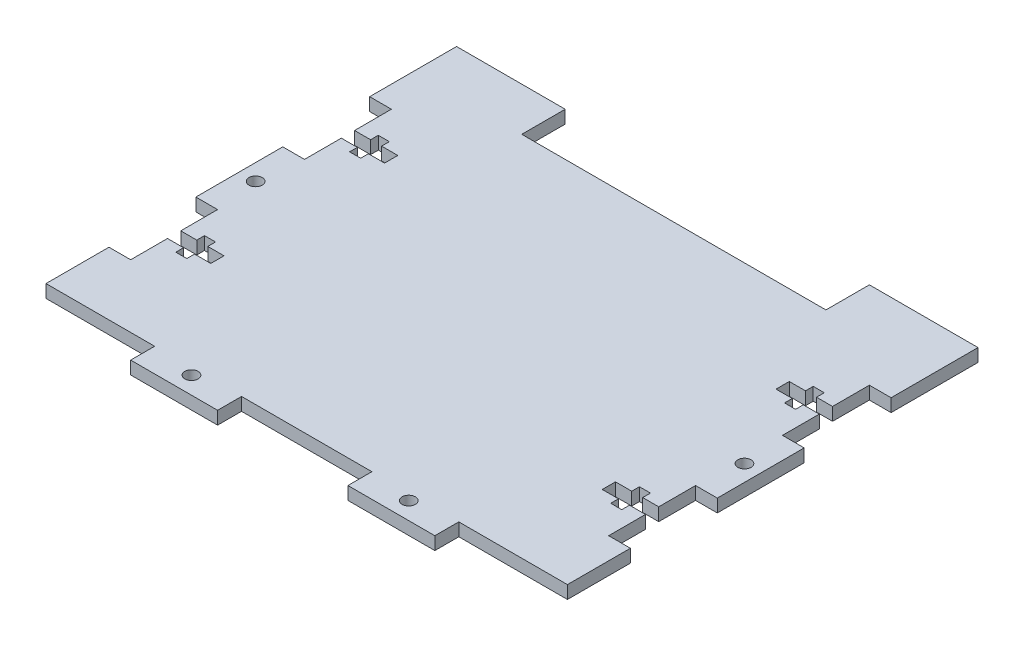
SolidWorks part; units mm, degrees
ref_plane "Front Plane" through (0, 0, 0) normal (0, 0, 1) x (1, 0, 0)
ref_plane "Top Plane" through (0, 0, 0) normal (0, 1, 0) x (1, 0, 0)
ref_plane "Right Plane" through (0, 0, 0) normal (1, 0, 0) x (0, 0, -1)
sketch "Sketch1" plane through (0, 0, 0) normal (0, 1, 0) x (1, 0, 0)
  line L1 (-60, -50) -> (60, -50)
  line L2 (-60, -50) -> (-60, 50)
  line L3 (-60, 50) -> (60, 50)
  line L4 (60, -50) -> (60, 50)
  line L5 (-60, -50) -> (60, 50) construction
  line L6 (-60, 50) -> (60, -50) construction
  point P0 (0, 0)
  dimension "D1" = 100
  dimension "D2" = 120
extrude "Boss-Extrude1" add sketch "Sketch1" along normal blind 2.9718
sketch "Sketch2" plane through (0, 2.9718, 0) normal (0, 1, 0) x (1, 0, 0)
  line L0 (60, 50) -> (-60, 50) construction
  line L1 (-35, 40) -> (35, 40)
  line L2 (-35, 40) -> (-35, 60)
  line L3 (-35, 60) -> (35, 60)
  line L4 (35, 40) -> (35, 60)
  line L5 (-35, 40) -> (35, 60) construction
  line L6 (-35, 60) -> (35, 40) construction
  point P0 (0, 50)
  dimension "D1" = 20
  dimension "D2" = 70
extrude "Cut-Extrude1" cut sketch "Sketch2" against normal through all
sketch "Sketch3" plane through (0, 2.9718, 0) normal (0, 1, 0) x (1, 0, 0)
  line L0 (-60, 50) -> (-60, -50) construction
  line L1 (-74.954, 18.476) -> (-45.046, 18.476)
  line L2 (-74.954, 18.476) -> (-74.954, 21.524)
  line L3 (-74.954, 21.524) -> (-45.046, 21.524)
  line L4 (-45.046, 18.476) -> (-45.046, 21.524)
  line L5 (-74.954, 18.476) -> (-45.046, 21.524) construction
  line L6 (-74.954, 21.524) -> (-45.046, 18.476) construction
  point P0 (-60, 20)
  point P7 (-60, 0)
  dimension "D1" = 3.048
  dimension "D2" = 29.908
  dimension "D3" = 20
extrude "Cut-Extrude2" cut sketch "Sketch3" against normal through all contours L3 L4 L1 L2
sketch "Sketch4" plane through (0, 2.9718, 0) normal (0, 1, 0) x (1, 0, 0)
  line L0 (-45.046, 20) -> (-74.954, 20) construction
  line L1 (-45.046, 18.476) -> (-45.046, 21.524) construction
  line L2 (-60, 18.476) -> (-60, -50) construction
  line L4 (-65, 10) -> (-55, 10)
  line L5 (-65, 10) -> (-65, 30)
  line L6 (-65, 30) -> (-55, 30)
  line L7 (-55, 10) -> (-55, 30)
  line L8 (-65, 10) -> (-55, 30) construction
  line L9 (-65, 30) -> (-55, 10) construction
  line L10 (-51.316, 16.698) -> (-48.776, 16.698)
  line L11 (-51.316, 16.698) -> (-51.316, 23.302)
  line L12 (-51.316, 23.302) -> (-48.776, 23.302)
  line L13 (-48.776, 16.698) -> (-48.776, 23.302)
  line L14 (-51.316, 16.698) -> (-48.776, 23.302) construction
  line L15 (-51.316, 23.302) -> (-48.776, 16.698) construction
  point P4 (-60, 20)
  point P7 (-60, 20)
  point P12 (-50.046, 20)
  dimension "D1" = 20
  dimension "D2" = 10
  dimension "D3" = 2.54
  dimension "D4" = 6.604
  dimension "D5" = 5
extrude "Cut-Extrude3" cut sketch "Sketch4" against normal blind 2.9718
mirror "Mirror1" about plane through (0, 0, 0) normal (0, 0, 1) of "Cut-Extrude3", "Cut-Extrude2"
mirror "Mirror2" about plane through (0, 0, 0) normal (1, 0, 0) of "Mirror1", "Cut-Extrude3", "Cut-Extrude2"
sketch "Sketch6" plane through (0, 2.9718, 0) normal (0, 1, 0) x (1, 0, 0)
  line L1 (-85, -55.5118) -> (-35, -55.5118)
  line L2 (-85, -55.5118) -> (-85, -44.4882)
  line L3 (-85, -44.4882) -> (-35, -44.4882)
  line L4 (-35, -55.5118) -> (-35, -44.4882)
  line L5 (-85, -55.5118) -> (-35, -44.4882) construction
  line L6 (-85, -44.4882) -> (-35, -55.5118) construction
  line L7 (0, -48.5852) -> (0, -63.0539) construction
  line L8 (85, -44.4882) -> (35, -55.5118) construction
  line L9 (85, -55.5118) -> (35, -44.4882) construction
  line L10 (35, -55.5118) -> (35, -44.4882)
  line L11 (85, -44.4882) -> (35, -44.4882)
  line L12 (85, -55.5118) -> (85, -44.4882)
  line L13 (85, -55.5118) -> (35, -55.5118)
  point P0 (-60, -50)
  point P13 (60, -50)
  dimension "D1" = 50
  dimension "D2" = 11.0236
extrude "Cut-Extrude4" cut sketch "Sketch6" against normal through all
sketch "Sketch7" plane through (0, 2.9718, 0) normal (0, 1, 0) x (1, 0, 0)
  line L0 (-35, -50) -> (35, -50) construction
  line L1 (-15, -55.5118) -> (15, -55.5118)
  line L2 (-15, -55.5118) -> (-15, -44.4882)
  line L3 (-15, -44.4882) -> (15, -44.4882)
  line L4 (15, -55.5118) -> (15, -44.4882)
  line L5 (-15, -55.5118) -> (15, -44.4882) construction
  line L6 (-15, -44.4882) -> (15, -55.5118) construction
  line L7 (-35, -44.4882) -> (-60, -44.4882) construction
  point P0 (0, -50)
  dimension "D1" = 20
extrude "Cut-Extrude6" cut sketch "Sketch7" against normal through all
sketch "Sketch8" plane through (0, 2.9718, 0) normal (0, 1, 0) x (1, 0, 0)
  line L0 (0, -44.4882) -> (0, -26.4278) construction
  line L1 (15, -44.4882) -> (-15, -44.4882) construction
  line L2 (-25, -50) -> (-25, -30.5228) construction
  line L3 (-35, -50) -> (-15, -50) construction
  circle A0 centre (-25, -46.0122) radius 1.524
  circle A1 centre (25, -46.0122) radius 1.524
  dimension "D1" = 3.048
  dimension "D2" = 1.524
extrude "Cut-Extrude7" cut sketch "Sketch8" against normal through all
sketch "Sketch11" plane through (0, 2.9718, 0) normal (0, 1, 0) x (1, 0, 0)
  line L0 (-60, 0) -> (-41.613, 0) construction
  line L1 (-60, 10) -> (-60, -10) construction
  line L2 (-45.046, 18.476) -> (-45.046, 21.524) construction
  line L3 (0, 0) -> (0, 11.8648) construction
  circle A0 centre (-56.2474, 0) radius 1.524
  circle A1 centre (56.2474, 0) radius 1.524
  dimension "D1" = 3.048
  dimension "D2" = 11.2014
extrude "Cut-Extrude8" cut sketch "Sketch11" against normal through all
